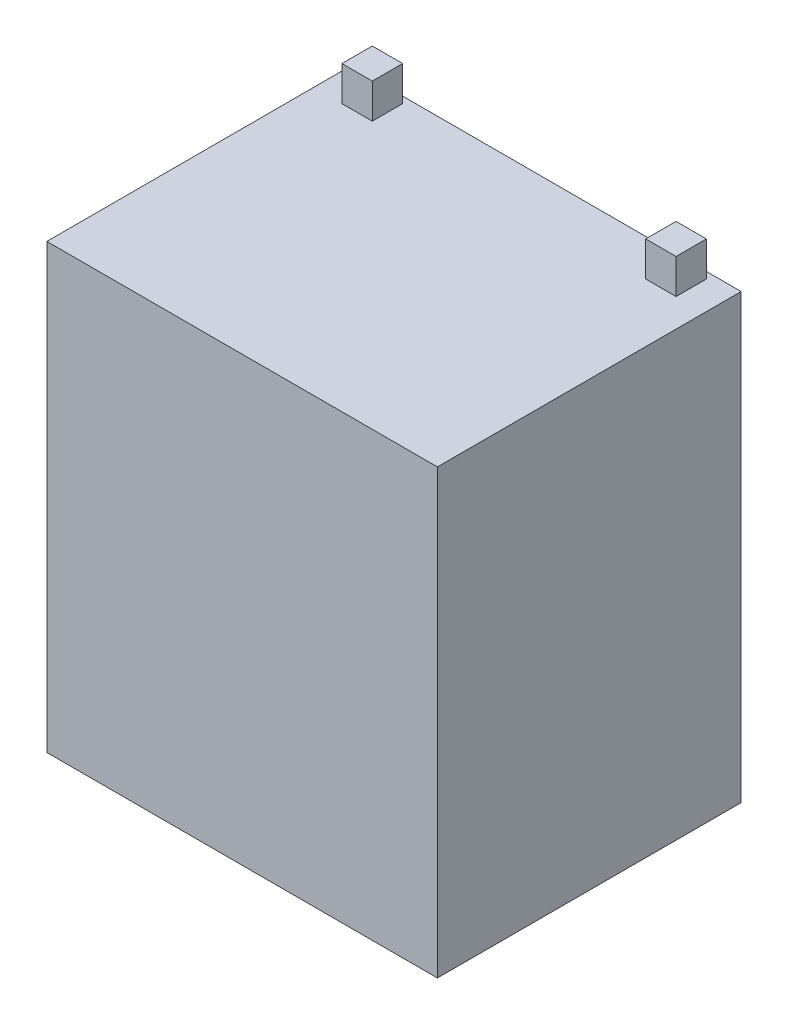
SolidWorks part; units mm, degrees
material "PVC rigide"
ref_plane "Plan de face" through (0, 0, 0) normal (0, 0, 1) x (1, 0, 0)
ref_plane "Plan de dessus" through (0, 0, 0) normal (0, 1, 0) x (1, 0, 0)
ref_plane "Plan de droite" through (0, 0, 0) normal (1, 0, 0) x (0, 0, -1)
sketch "Esquisse1" plane through (0, 0, 0) normal (0, 1, 0) x (1, 0, 0)
  line L1 (-45, -35) -> (45, -35)
  line L2 (-45, -35) -> (-45, 35)
  line L3 (-45, 35) -> (45, 35)
  line L4 (45, -35) -> (45, 35)
  line L5 (-45, -35) -> (45, 35) construction
  line L6 (-45, 35) -> (45, -35) construction
  point P0 (0, 0)
  dimension "D1" = 90
  dimension "D2" = 70
extrude "Boss.-Extru.1" add sketch "Esquisse1" along normal blind 102
sketch "Esquisse2" plane through (0, 102, 0) normal (0, 1, 0) x (1, 0, 0)
  line L0 (0, 35) -> (0, -35) construction
  line L1 (45, 35) -> (-45, 35) construction
  line L2 (-45, -35) -> (45, -35) construction
  line L3 (38.5, 26.5) -> (31.5, 26.5)
  line L4 (-45, 35) -> (-45, -35) construction
  line L5 (-45, 0) -> (45, 0) construction
  line L6 (45, -35) -> (45, 35) construction
  line L7 (-38.5, 33.5) -> (-31.5, 33.5)
  line L8 (-38.5, 33.5) -> (-38.5, 26.5)
  line L9 (-38.5, 26.5) -> (-31.5, 26.5)
  line L10 (-31.5, 33.5) -> (-31.5, 26.5)
  line L11 (-38.5, 33.5) -> (-31.5, 26.5) construction
  line L12 (-38.5, 26.5) -> (-31.5, 33.5) construction
  line L13 (38.5, 33.5) -> (38.5, 26.5)
  line L14 (38.5, 33.5) -> (31.5, 33.5)
  line L15 (31.5, 33.5) -> (31.5, 26.5)
  point P6 (-35, 30)
  dimension "D1" = 30
  dimension "D2" = 35
  dimension "D3" = 7
  dimension "D4" = 7
extrude "Boss.-Extru.2" add sketch "Esquisse2" along normal blind 8
